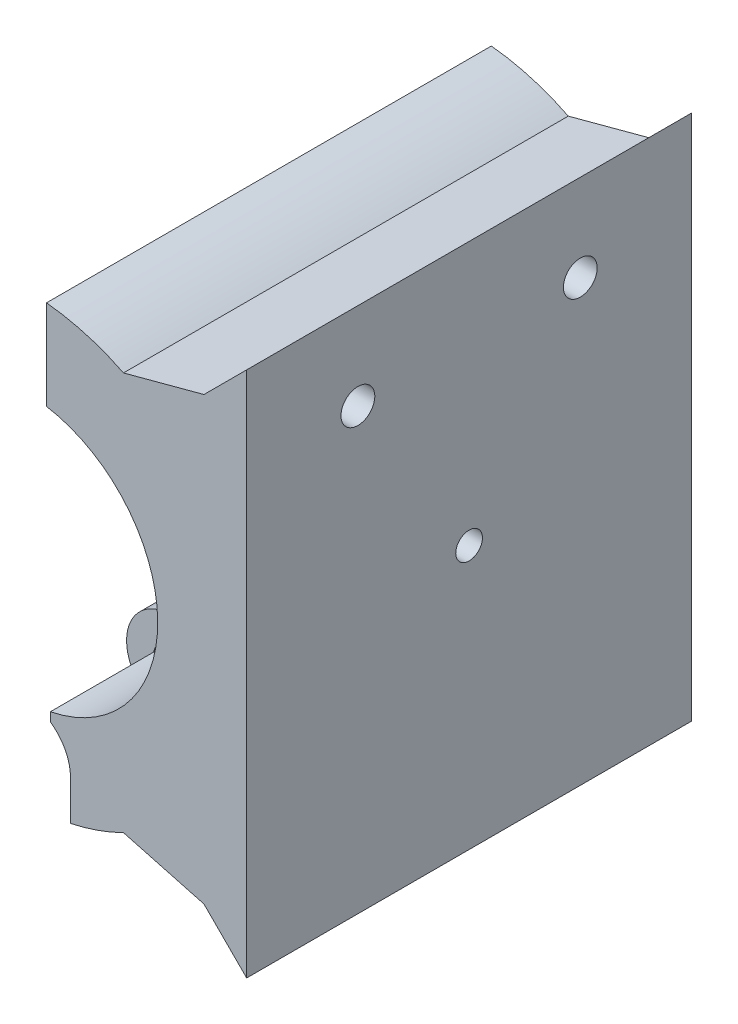
SolidWorks part; units mm, degrees
ref_plane "Front Plane" through (0, 0, 0) normal (0, 0, 1) x (1, 0, 0)
ref_plane "Top Plane" through (0, 0, 0) normal (0, 1, 0) x (1, 0, 0)
ref_plane "Right Plane" through (0, 0, 0) normal (1, 0, 0) x (0, 0, -1)
sketch "Sketch1" plane through (0, 0, 0) normal (0, 0, 1) x (1, 0, 0)
  line L0 (0, 72.5599) -> (0, -72.3751) construction
  line L1 (-109.2559, 0) -> (117.0202, 0) construction
  line L3 (2.5, 14.7902) -> (2.5, 24.8747)
  arc A0 (0, -25) -> (2.5, 24.8747) centre (0, 0) ccw
  arc A1 (0, -15) -> (2.5, 14.7902) centre (0, 0) ccw
  circle A2 centre (0, -20) radius 5
  circle A3 centre (0, -20) radius 2
  dimension "D1" = 25
  dimension "D2" = 15
  dimension "D4" = 10
  dimension "D5" = 4
  dimension "D6" = 20
extrude "Boss-Extrude1" add sketch "Sketch1" along normal blind 50
sketch "Sketch14" plane through (0, 0, 0) normal (1, 0, 0) x (0, 0, -1)
  line L0 (0, 0) -> (-25, 0) construction
  dimension "D1" = 25
ref_plane "Plane2" through (0, 0, 25) normal (0, 0, -1) x (-1, 0, 0)
ref_plane "Plane1" through (0, -15, 50) normal (0, 0, -1) x (-1, 0, 0)
sketch "Sketch16" plane through (0, 0, 50) normal (0, 0, 1) x (1, 0, 0)
  line L0 (0, -25.2) -> (5.2, -25.2)
  line L1 (5.2, -25.2) -> (5.2, -20)
  arc A0 (5.2, -20) -> (0, -25.2) centre (0, -20) ccw
  dimension "D1" = 5.2
extrude "Cut-Extrude13" cut sketch "Sketch16" against normal blind 16.5
mirror "Mirror2" about plane through (0, 0, 25) normal (0, 0, -1) of "Cut-Extrude13"
sketch "Sketch17" plane through (0, 0, 0) normal (0, 0, -1) x (-1, 0, 0)
  line L1 (-20.2, 24.8) -> (-11.151, 22.3753)
  line L2 (0, 0) -> (-20.2, 0) construction
  line L3 (-20.2, 24.8) -> (-25, 29.6)
  line L6 (-20.2, 24.8) -> (-20.2, 0) construction
  line L7 (-25, 29.6) -> (-25, -29.6)
  line L8 (-20.2, 0) -> (-25, 0) construction
  line L9 (-20.2, -24.8) -> (-25, -29.6)
  line L10 (-20.2, -24.8) -> (-11.151, -22.3753)
  line L11 (-11.151, 22.3753) -> (-20.2, 0)
  line L12 (-20.2, 0) -> (-11.151, -22.3753)
  arc A1 (-2.5, 24.8747) -> (-5.2, -24.4532) centre (0, 0) ccw construction
  arc A2 (-11.151, -22.3753) -> (-11.151, 22.3753) centre (0, 0) cw construction
  point P3 (-25, 0)
  dimension "D5" = 24.8
  dimension "D1" = 75
  dimension "D2" = 45
  dimension "D3" = 20.2
  dimension "D4" = 4.8
extrude "Boss-Extrude2" add sketch "Sketch17" against normal up to surface (50 mm away) up to face at (10.3479, -3.6909, 50)
sketch "Sketch13" plane through (2.5, 0, 0) normal (-1, 0, 0) x (0, 0, 1)
  line L0 (25, 24.8747) -> (50, 24.8747) construction
  line L2 (50, 24.8747) -> (0, 24.8747) construction
  line L3 (37.5, 24.8747) -> (37.5, 14.7902) construction
  line L4 (25, 24.8747) -> (0, 24.8747) construction
  line L5 (50, 14.7902) -> (0, 14.7902) construction
  line L6 (12.5, 24.8747) -> (12.5, 14.7902) construction
  circle A0 centre (37.5, 19.8324) radius 1.9
  circle A1 centre (12.5, 19.8324) radius 1.9
  dimension "D1" = 3.8
  dimension "D2" = 3.8
extrude "Cut-Extrude12" cut sketch "Sketch13" against normal through all
sketch "Sketch19" plane through (0, 0, 50) normal (0, 0, 1) x (1, 0, 0)
  line L0 (2.9379, -15.7095) -> (2.9379, -14.7095)
  arc A4 (1.2359, -14.949) -> (2.9379, -15.7095) centre (0, -20) cw
  arc A5 (1.2359, -14.949) -> (2.5, 14.7902) centre (0, 0) ccw construction
  arc A6 (5.2, -20) -> (1.2359, -14.949) centre (0, -20) ccw construction
  arc A7 (1.2359, -14.949) -> (2.9379, -14.7095) centre (0, 0) ccw
  dimension "D1" = 1
extrude "Cut-Extrude14" cut sketch "Sketch19" against normal blind 16.5
mirror "Mirror4" about plane through (0, 0, 25) normal (0, 0, -1) of "Cut-Extrude14"
sketch "Sketch20" plane through (0, 0, 0) normal (1, 0, 0) x (0, 0, -1)
  line L0 (0, 0) -> (-25, 0) construction
  circle A0 centre (-25, 0) radius 1.5
  dimension "D2" = 3
  dimension "D1" = 25
extrude "Cut-Extrude15" cut sketch "Sketch20" along normal through all
